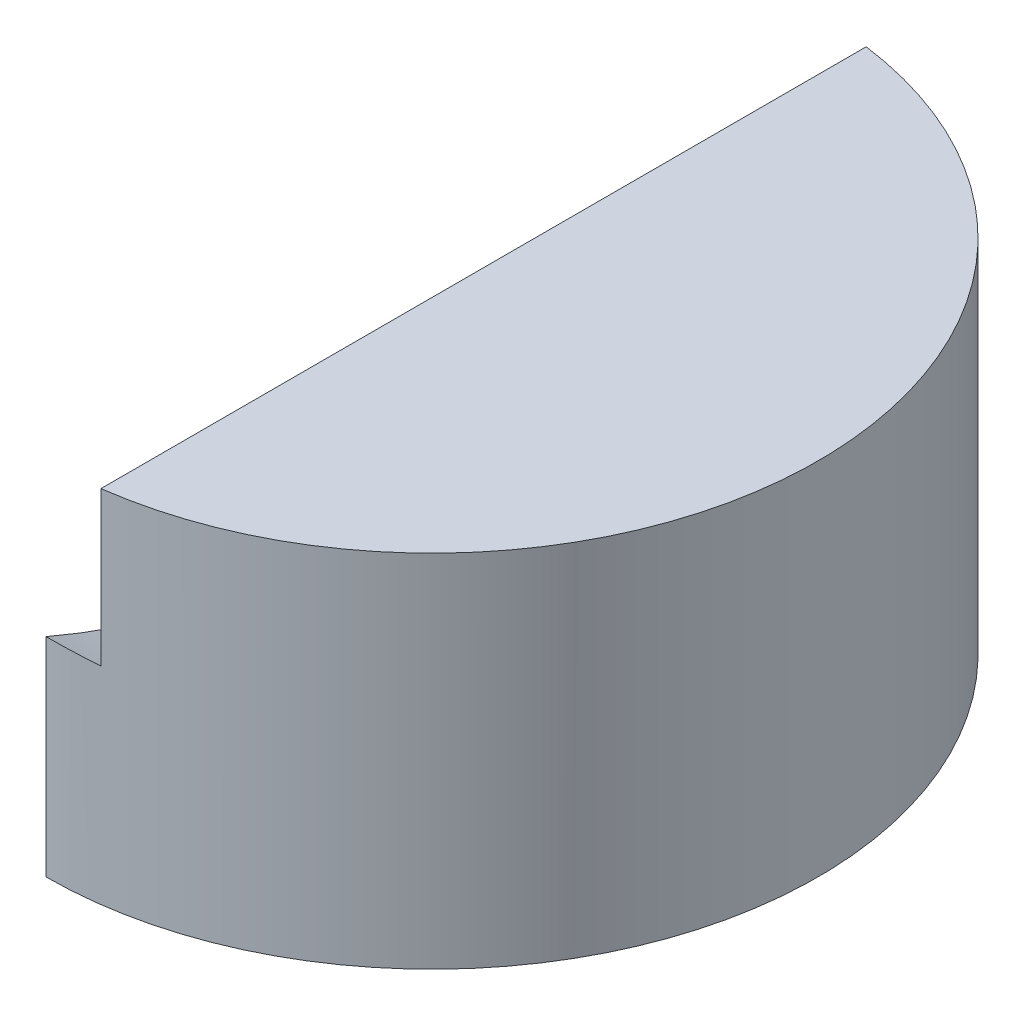
SolidWorks part; units mm, degrees
ref_plane "Front Plane" through (0, 0, 0) normal (0, 0, 1) x (1, 0, 0)
ref_plane "Top Plane" through (0, 0, 0) normal (0, 1, 0) x (1, 0, 0)
ref_plane "Right Plane" through (0, 0, 0) normal (1, 0, 0) x (0, 0, -1)
sketch "Sketch1" plane through (0, 0, 0) normal (0, 1, 0) x (1, 0, 0)
  line L0 (0, 75) -> (0, -75)
  circle A0 centre (0, 0) radius 75
  dimension "D1" = 150
extrude "Boss-Extrude2" add sketch "Sketch1" along normal blind 100 contours L0 A0
sketch "Sketch3" plane through (0, 0, 0) normal (0, -1, 0) x (-1, 0, 0)
  line L0 (0, 0) -> (-75, 0) construction
  line L2 (-54, 0) -> (-65, 0)
  line L3 (-54, 0) -> (-54, 22)
  line L4 (-54, 22) -> (-65, 22)
  line L5 (-65, 0) -> (-65, 22)
  arc A0 (0, 75) -> (0, -75) centre (0, 0) ccw construction
  dimension "D1" = 10
  dimension "D2" = 11
  dimension "D3" = 22
revolve "Cut-Revolve3" cut sketch "Sketch3" angle 360 about L0
sketch "Sketch4" plane through (65, 0, 0) normal (-1, 0, 0) x (0, 0, 1)
  line L0 (22, 0) -> (-22, 0) construction
  circle A0 centre (0, 0) radius 1
  dimension "D1" = 2
extrude "Cut-Extrude1" cut sketch "Sketch4" against normal blind 2
sketch "Sketch5" plane through (54, 0, 0) normal (1, 0, 0) x (0, 0, -1)
  line L0 (22, 0) -> (-22, 0) construction
  circle A0 centre (0, 0) radius 1
  dimension "D1" = 2
extrude "Cut-Extrude2" cut sketch "Sketch5" against normal blind 2
pattern_circular "CirPattern1" count 4 every 90 about axis through (0, 0, 0) along (0, 1, 0) of "Cut-Revolve3", "Cut-Extrude1", "Cut-Extrude2"
sketch "Sketch6" plane through (0, 100, 0) normal (0, 1, 0) x (1, 0, 0)
  line L0 (0, 75) -> (0, -75) construction
  line L1 (0, 0) -> (10, 0)
  line L2 (0, 0) -> (0, -190)
  line L3 (0, -190) -> (10, -190)
  line L4 (10, 0) -> (10, -190)
  dimension "D1" = 10
  dimension "D2" = 190
sketch "Sketch8" plane through (0, 0, 0) normal (-1, 0, 0) x (0, 0, 1)
  line L0 (-75, 0) -> (-67, 0) construction
  line L1 (-75, 100) -> (-75, 0) construction
  line L2 (0, -1000) -> (0, 49000) construction
  line L3 (-52, 0) -> (52, 0) construction
  line L4 (-40, 5) -> (-20, 5)
  line L5 (-40, 5) -> (-40, 0)
  line L6 (-40, 0) -> (-20, 0)
  line L7 (-20, 5) -> (-20, 0)
  line L8 (40, 0) -> (20, 0)
  line L9 (20, 5) -> (20, 0)
  line L10 (40, 5) -> (20, 5)
  line L11 (40, 5) -> (40, 0)
  circle A0 centre (-70, 10) radius 2.5
  circle A1 centre (70, 10) radius 2.5
  dimension "D1" = 5
  dimension "D2" = 10
  dimension "D3" = 5
  dimension "D4" = 20
  dimension "D5" = 5
  dimension "D6" = 20
extrude "Boss-Extrude4" add sketch "Sketch6" along normal blind 115
sketch "Sketch10" plane through (0, 215, 0) normal (0, 1, 0) x (1, 0, 0)
  line L1 (10, 0) -> (0, 0)
  line L2 (10, 0) -> (10, -190)
  line L3 (10, -190) -> (0, -190)
  line L4 (0, 0) -> (0, -190)
revolve "Cut-Revolve4" cut sketch "Sketch10" angle 360 about L1
sketch "Sketch11" plane through (10, 0, 0) normal (-1, 0, 0) x (0, 0, 1)
  line L0 (74.3303, 40.1429) -> (74.3303, 100) construction
  line L1 (-74.3303, 100) -> (74.3303, 100) construction
  circle A0 centre (-0.6697, 47.5) radius 1
  circle A1 centre (-65.6697, 60.5) radius 1
  circle A2 centre (64.3303, 60.5) radius 1
  arc A3 (-74.3303, 40.1429) -> (74.3303, 40.1429) centre (0, 215) ccw construction
  circle A4 centre (-0.6697, 228.3541) radius 200.0539 construction
  dimension "D3" = 2
  dimension "D7" = 2
  dimension "D8" = 2
  dimension "D1" = 75
  dimension "D2" = 52.5
  dimension "D4" = 167.5
  dimension "D5" = 180
  dimension "D6" = 180
  dimension "D9" = 65
  dimension "D10" = 13
  dimension "D11" = 65
  dimension "D12" = 13
extrude "Cut-Extrude3" cut sketch "Sketch11" against normal blind 2
extrude "Cut-Extrude4" cut sketch "Sketch8" against normal blind 10
sketch "Sketch12" plane through (0, 100, 0) normal (0, 1, 0) x (1, 0, 0)
  circle A0 centre (0, 0) radius 75
  dimension "D1" = 150
extrude "Cut-Extrude5" cut sketch "Sketch12" against normal blind 30
